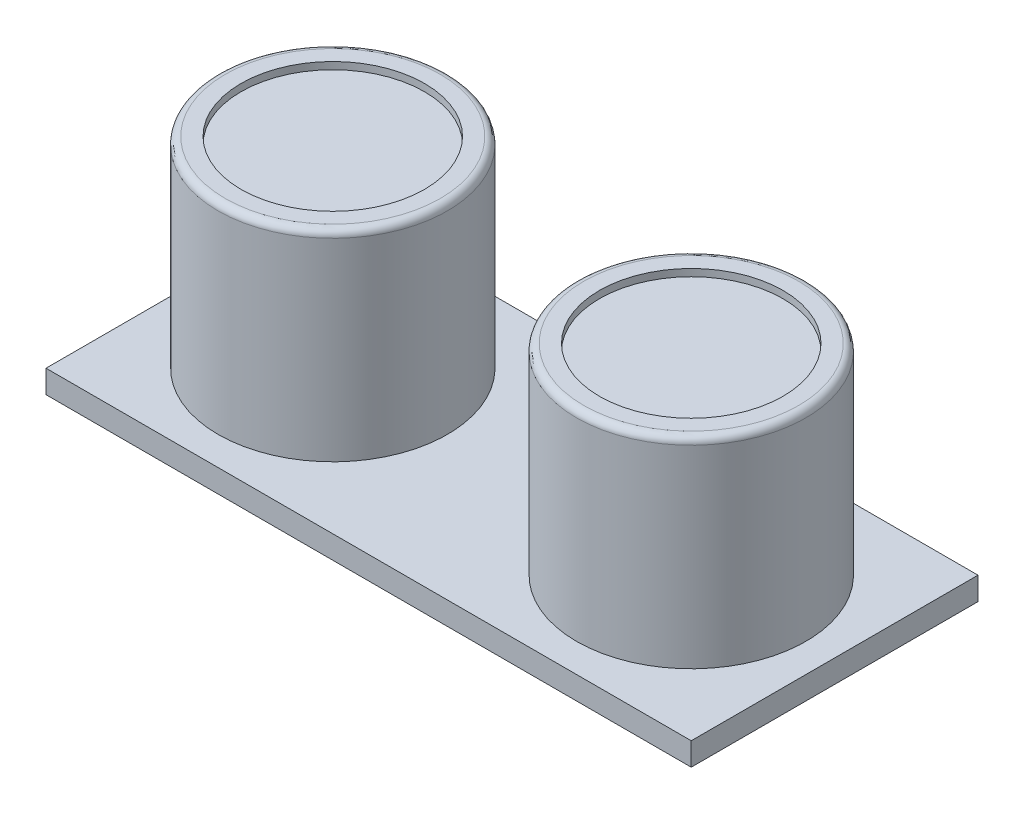
SolidWorks part; units mm, degrees
ref_plane "Front Plane" through (0, 0, 0) normal (0, 0, 1) x (1, 0, 0)
ref_plane "Top Plane" through (0, 0, 0) normal (0, 1, 0) x (1, 0, 0)
ref_plane "Right Plane" through (0, 0, 0) normal (1, 0, 0) x (0, 0, -1)
sketch "Sketch1" plane through (0, 0, 0) normal (0, 1, 0) x (1, 0, 0)
  line L1 (0, 0) -> (45, 0)
  line L2 (0, 0) -> (0, 20)
  line L3 (0, 20) -> (45, 20)
  line L4 (45, 0) -> (45, 20)
  dimension "D1" = 45
  dimension "D2" = 20
extrude "Boss-Extrude1" add sketch "Sketch1" along normal blind 1.6
sketch "Sketch2" plane through (0, 1.6, 0) normal (0, 1, 0) x (1, 0, 0)
  line L0 (45, 0) -> (45, 20) construction
  line L1 (10, 10) -> (35, 10) construction
  line L2 (45, 20) -> (0, 20) construction
  circle A0 centre (10, 10) radius 8
  circle A1 centre (35, 10) radius 8
  point P7 (45, 10)
  point P9 (22.5, 20)
  point P10 (22.5, 10)
  dimension "D1" = 16
  dimension "D2" = 25
extrude "Boss-Extrude2" add sketch "Sketch2" along normal blind 14
sketch "Sketch3" plane through (0, 15.6, 0) normal (0, 1, 0) x (1, 0, 0)
  circle A0 centre (10, 10) radius 6.4
  circle A1 centre (35, 10) radius 6.4
  circle A2 centre (35, 10) radius 8 construction
  circle A3 centre (10, 10) radius 8 construction
  dimension "D1" = 1.6
  dimension "D2" = 1.6
extrude "Cut-Extrude1" cut sketch "Sketch3" against normal blind 0.5
fillet "Fillet1" radius 0.5 2 edges at (35, 15.6, -2) (10, 15.6, -2)
